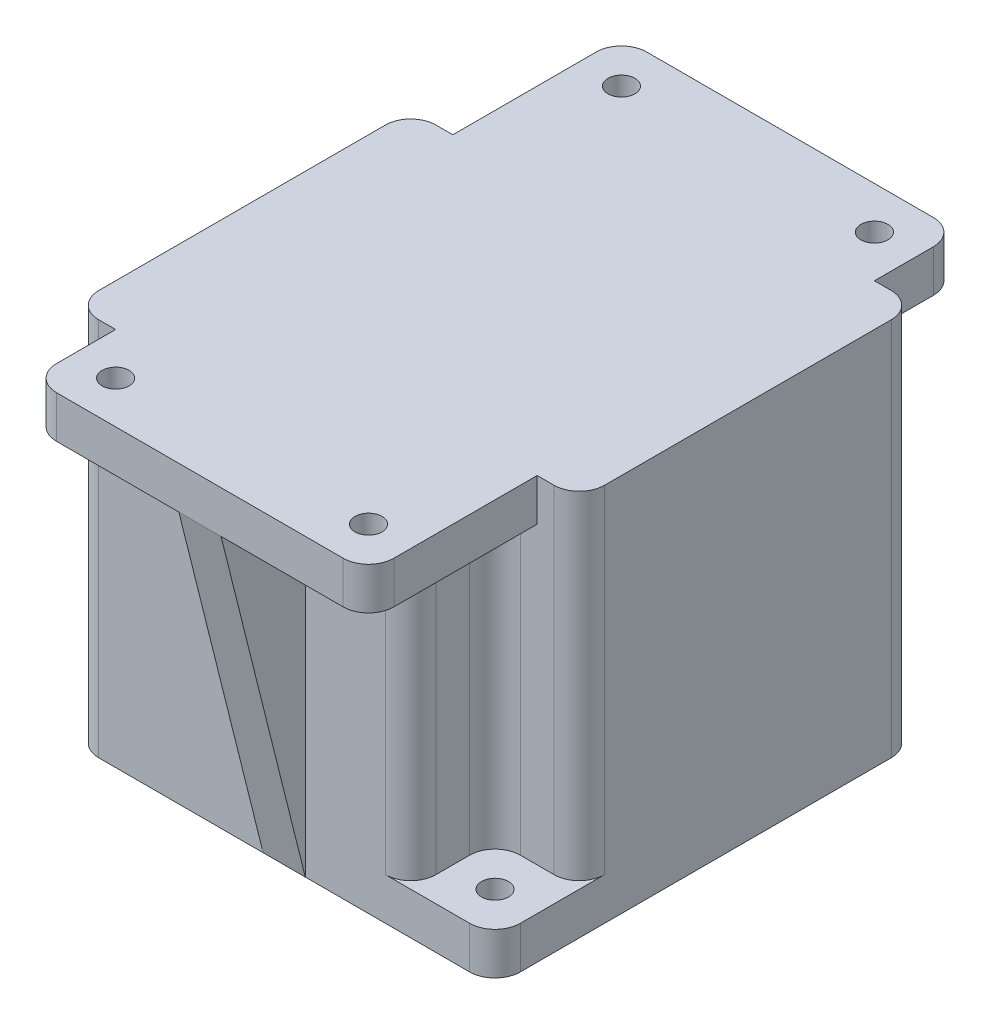
SolidWorks part; units mm, degrees
ref_plane "Plan de face" through (0, 0, 0) normal (0, 0, 1) x (1, 0, 0)
ref_plane "Plan de dessus" through (0, 0, 0) normal (0, 1, 0) x (1, 0, 0)
ref_plane "Plan de droite" through (0, 0, 0) normal (1, 0, 0) x (0, 0, -1)
sketch "Esquisse1" plane through (0, 0, 0) normal (0, 1, 0) x (1, 0, 0)
  line L0 (-20, 20) -> (20, 20) construction
  line L1 (-25, -25) -> (25, -25)
  line L2 (-25, -25) -> (-25, 25)
  line L3 (-25, 25) -> (25, 25)
  line L4 (25, -25) -> (25, 25)
  line L5 (-25, -25) -> (25, 25) construction
  line L6 (-25, 25) -> (25, -25) construction
  circle A0 centre (-20, 20) radius 1.6
  circle A1 centre (20, -20) radius 1.6
  point P0 (0, 0)
  dimension "D2" = 40
  dimension "D4" = 3.2
  dimension "D1" = 50
  dimension "D3" = 40
extrude "Boss.-Extru.1" add sketch "Esquisse1" along normal blind 45
fillet "Congé1" radius 3 4 edges at (-25, 22.5, -25) (-25, 22.5, 25) (25, 22.5, -25) (25, 22.5, 25)
sketch "Esquisse2" plane through (0, 45, 0) normal (0, 1, 0) x (1, 0, 0)
  line L0 (22, 25) -> (-22, 25) construction
  line L1 (-15, 15) -> (-25, 15)
  line L2 (-15, 15) -> (-15, 25)
  line L3 (-15, 25) -> (-25, 25)
  line L4 (-25, 15) -> (-25, 25)
  line L5 (-15, 15) -> (-25, 25) construction
  line L6 (-15, 25) -> (-25, 15) construction
  line L8 (15, -15) -> (25, -15)
  line L9 (15, -15) -> (15, -25)
  line L10 (15, -25) -> (25, -25)
  line L11 (25, -15) -> (25, -25)
  line L12 (15, -15) -> (25, -25) construction
  line L13 (15, -25) -> (25, -15) construction
  point P0 (-20, 20)
  point P9 (20, -20)
extrude "Enlèv. mat.-Extru.1" cut sketch "Esquisse2" against normal blind 40
fillet "Congé2" [suppressed] radius 3
sketch "Esquisse3" [suppressed] plane through (0, 42.5, 0) normal (0, -1, 0) x (1, 0, 0)
  line L0 (24.1213, 24.1213) -> (15.8787, 15.8787) construction
  line L1 (22.6536, 22.6536) -> (19.0287, 23.6249)
  line L2 (19.0287, 23.6249) -> (16.3751, 20.9713)
  line L3 (16.3751, 20.9713) -> (17.3464, 17.3464)
  line L4 (17.3464, 17.3464) -> (20.9713, 16.3751)
  line L5 (20.9713, 16.3751) -> (23.6249, 19.0287)
  line L6 (23.6249, 19.0287) -> (22.6536, 22.6536)
  line L7 (-15.8787, -15.8787) -> (-24.1213, -24.1213) construction
  line L9 (-22.6536, -22.6536) -> (-19.0287, -23.6249)
  line L10 (-19.0287, -23.6249) -> (-16.3751, -20.9713)
  line L11 (-16.3751, -20.9713) -> (-17.3464, -17.3464)
  line L12 (-17.3464, -17.3464) -> (-20.9713, -16.3751)
  line L13 (-20.9713, -16.3751) -> (-23.6249, -19.0287)
  line L14 (-23.6249, -19.0287) -> (-22.6536, -22.6536)
  circle A0 centre (20, 20) radius 3.25 construction
  arc A1 (25, 22) -> (22, 25) centre (22, 22) ccw construction
  arc A2 (15, 18) -> (18, 15) centre (18, 18) ccw construction
  arc A3 (-15, -18) -> (-18, -15) centre (-18, -18) ccw construction
  arc A4 (-25, -22) -> (-22, -25) centre (-22, -22) ccw construction
  circle A5 centre (-20, -20) radius 3.25 construction
  dimension "D1" = 6.5
  dimension "D2" = 6.5
extrude "Enlèv. mat.-Extru.2" [suppressed] cut sketch "Esquisse3" against normal blind 2.5
sketch "Esquisse4" plane through (0, 45, 0) normal (0, 1, 0) x (1, 0, 0)
  line L1 (-15, -30) -> (15, -30) construction
  line L2 (-15, -30) -> (-15, 30) construction
  line L3 (-15, 30) -> (15, 30) construction
  line L4 (15, -30) -> (15, 30) construction
  line L5 (-15, -30) -> (15, 30) construction
  line L6 (-15, 30) -> (15, -30) construction
  line L7 (20, -35) -> (-20, -35)
  line L8 (20, -35) -> (20, 35)
  line L9 (20, 35) -> (-20, 35)
  line L10 (-20, -35) -> (-20, 35)
  line L11 (20, -35) -> (-20, 35) construction
  line L12 (20, 35) -> (-20, -35) construction
  circle A0 centre (-15, 30) radius 1.6
  circle A1 centre (15, 30) radius 1.6
  circle A2 centre (15, -30) radius 1.6
  circle A3 centre (-15, -30) radius 1.6
  point P0 (0, 0)
  point P10 (0, 0)
  dimension "D1" = 3.2
  dimension "D2" = 30
  dimension "D3" = 60
  dimension "D4" = 5
  dimension "D5" = 5
extrude "Boss.-Extru.2" add sketch "Esquisse4" against normal blind 5
fillet "Congé3" radius 3 4 edges at (20, 42.5, 35) (-20, 42.5, 35) (20, 42.5, -35) (-20, 42.5, -35)
fillet "Congé4" radius 3 6 edges at (-25, 25, -15) (-15, 22.5, -25) (-15, 22.5, -15) (15, 22.5, 25) (15, 22.5, 15) (25, 25, 15)
fillet "Congé5" [suppressed] radius 3
sketch "Esquisse5" plane through (0, 40, 0) normal (0, -1, 0) x (1, 0, 0)
  line L1 (-15, -30) -> (15, -30) construction
  line L2 (-15, -30) -> (-15, 30) construction
  line L3 (-15, 30) -> (15, 30) construction
  line L4 (15, -30) -> (15, 30) construction
  line L5 (-15, -30) -> (15, 30) construction
  line L6 (-15, 30) -> (15, -30) construction
  line L7 (-13.5541, 27.1082) -> (-11.7726, 29.8063)
  line L8 (-11.7726, 29.8063) -> (-13.2186, 32.6981)
  line L9 (-13.2186, 32.6981) -> (-16.4459, 32.8918)
  line L10 (-16.4459, 32.8918) -> (-18.2274, 30.1937)
  line L11 (-18.2274, 30.1937) -> (-16.7814, 27.3019)
  line L12 (-16.7814, 27.3019) -> (-13.5541, 27.1082)
  line L13 (13.296, 26.592) -> (17.0994, 26.8203)
  line L14 (17.0994, 26.8203) -> (18.8034, 30.2283)
  line L15 (18.8034, 30.2283) -> (16.704, 33.408)
  line L16 (16.704, 33.408) -> (12.9006, 33.1797)
  line L17 (12.9006, 33.1797) -> (11.1966, 29.7717)
  line L18 (11.1966, 29.7717) -> (13.296, 26.592)
  line L19 (13.296, -26.592) -> (11.1966, -29.7717)
  line L20 (11.1966, -29.7717) -> (12.9006, -33.1797)
  line L21 (12.9006, -33.1797) -> (16.704, -33.408)
  line L22 (16.704, -33.408) -> (18.8034, -30.2283)
  line L23 (18.8034, -30.2283) -> (17.0994, -26.8203)
  line L24 (17.0994, -26.8203) -> (13.296, -26.592)
  line L25 (-13.296, -26.592) -> (-17.0994, -26.8203)
  line L26 (-17.0994, -26.8203) -> (-18.8034, -30.2283)
  line L27 (-18.8034, -30.2283) -> (-16.704, -33.408)
  line L28 (-16.704, -33.408) -> (-12.9006, -33.1797)
  line L29 (-12.9006, -33.1797) -> (-11.1966, -29.7717)
  line L30 (-11.1966, -29.7717) -> (-13.296, -26.592)
  circle A0 centre (-15, 30) radius 2.8 construction
  circle A1 centre (15, 30) radius 3.2998 construction
  circle A2 centre (15, -30) radius 3.2998 construction
  circle A3 centre (-15, -30) radius 3.2998 construction
  point P0 (0, 0)
  dimension "D1" = 5.6
extrude "Enlèv. mat.-Extru.3" cut sketch "Esquisse5" against normal blind 2.5
sketch "Esquisse6" plane through (0, 0, 0) normal (1, 0, 0) x (0, 0, -1)
  line L0 (-35, 40) -> (-25, 0)
  line L1 (-25, 0) -> (-25, 40)
  line L2 (-25, 40) -> (-35, 40)
  line L3 (35, 40) -> (25, 0)
  line L4 (25, 0) -> (25, 40)
  line L5 (25, 40) -> (35, 40)
extrude "Boss.-Extru.3" add sketch "Esquisse6" along normal blind 2.5 and the other way blind 2.5
